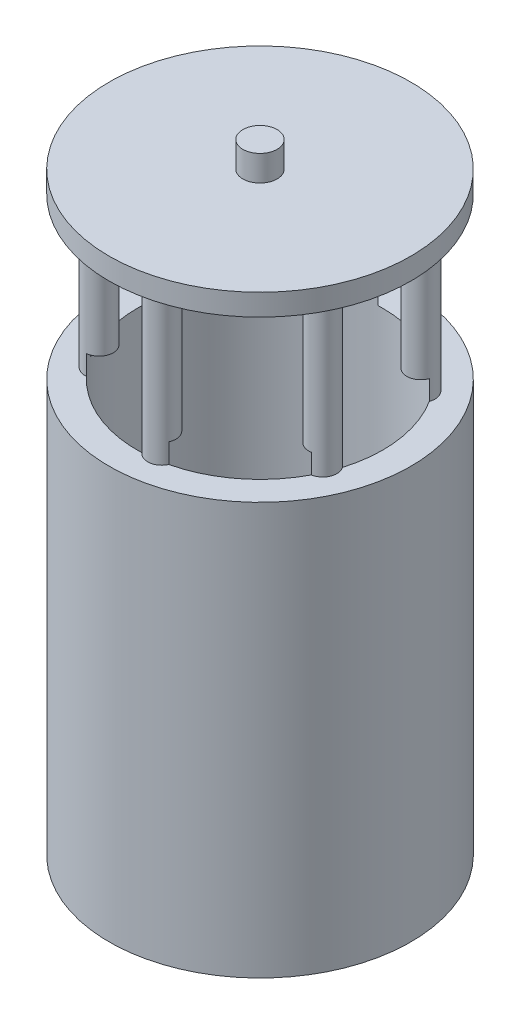
SolidWorks part; units mm, degrees
ref_plane "Front Plane" through (0, 0, 0) normal (0, 0, 1) x (1, 0, 0)
ref_plane "Top Plane" through (0, 0, 0) normal (0, 1, 0) x (1, 0, 0)
ref_plane "Right Plane" through (0, 0, 0) normal (1, 0, 0) x (0, 0, -1)
sketch "Sketch1" plane through (0, 0, 0) normal (0, 1, 0) x (1, 0, 0)
  circle A0 centre (0, 0) radius 27.955
  dimension "D1" = 55.91
extrude "Boss-Extrude1" add sketch "Sketch1" along normal blind 4
sketch "Sketch2" plane through (0, 4, 0) normal (0, 1, 0) x (1, 0, 0)
  circle A0 centre (0, 0) radius 3.175
  dimension "D1" = 6.35
extrude "Boss-Extrude2" add sketch "Sketch2" along normal blind 4.76
sketch "Sketch3" plane through (0, 0, 0) normal (0, -1, 0) x (1, 0, 0)
  circle A0 centre (0, 0) radius 21.2558
  circle A1 centre (2.874, 21.0606) radius 2.6153
  circle A2 centre (19.6761, 8.0413) radius 2.6153
  circle A3 centre (16.802, -13.0193) radius 2.6153
  circle A4 centre (-2.874, -21.0606) radius 2.6153
  circle A5 centre (-19.6761, -8.0413) radius 2.6153
  circle A6 centre (-16.802, 13.0193) radius 2.6153
  point P17 (0, 0)
  dimension "D1" = 6
extrude "Boss-Extrude3" add sketch "Sketch3" along normal blind 29.718 contours A0 A4 | A0 A4 | A0 A3 | A0 A3 | A0 A2 | A0 A2 | A0 A1 | A0 A1 | A0 A6 | A0 A6 | A0 A5 | A0 A5
sketch "Sketch4" plane through (0, -29.718, 0) normal (0, -1, 0) x (1, 0, 0)
  circle A0 centre (0, 0) radius 27.955
extrude "Boss-Extrude4" add sketch "Sketch4" along normal blind 76.35
sketch "Sketch5" plane through (0, -106.068, 0) normal (0, -1, 0) x (1, 0, 0)
  circle A0 centre (0, 0) radius 22.7587
extrude "Cut-Extrude1" cut sketch "Sketch5" against normal blind 80
